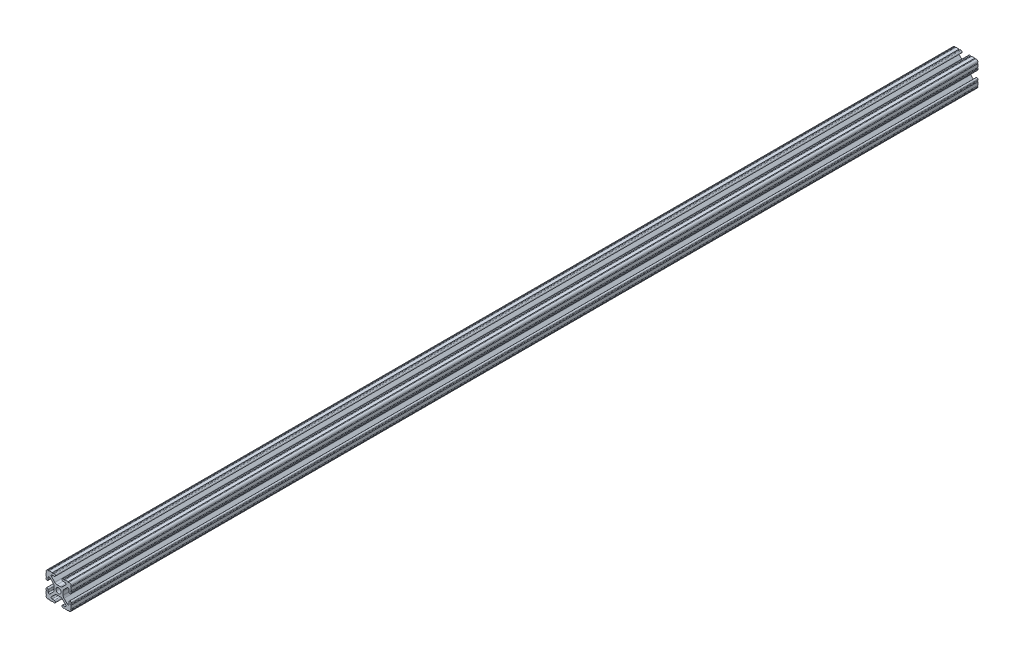
SolidWorks part; units mm, degrees
ref_plane "Front Plane" through (0, 0, 0) normal (0, 0, 1) x (1, 0, 0)
ref_plane "Top Plane" through (0, 0, 0) normal (0, 1, 0) x (1, 0, 0)
ref_plane "Right Plane" through (0, 0, 0) normal (1, 0, 0) x (0, 0, -1)
sketch "Sketch1" plane through (0, 0, 0) normal (0, 0, 1) x (1, 0, 0)
  line L0 (-12.7, -6.3331) -> (-12.7, -9.5504)
  line L1 (-9.5504, -12.7) -> (-6.3331, -12.7)
  line L2 (-5.3171, -12.7) -> (-4.3434, -12.7)
  line L3 (-4.3434, -10.4902) -> (-6.4748, -10.4902)
  line L4 (-7.1932, -8.7558) -> (-3.8632, -5.4257)
  line L5 (-1.6181, -4.4958) -> (1.6181, -4.4958)
  line L6 (3.8632, -5.4257) -> (7.1932, -8.7558)
  line L7 (6.4748, -10.4902) -> (4.3434, -10.4902)
  line L8 (4.3434, -12.7) -> (5.3171, -12.7)
  line L9 (6.3331, -12.7) -> (9.5504, -12.7)
  line L10 (12.7, -9.5504) -> (12.7, -6.3331)
  line L11 (12.7, -5.3171) -> (12.7, -4.3434)
  line L12 (10.4902, -4.3434) -> (10.4902, -6.4748)
  line L13 (8.7558, -7.1932) -> (5.4257, -3.8632)
  line L14 (4.4958, -1.6181) -> (4.4958, 1.6181)
  line L15 (5.4257, 3.8632) -> (8.7558, 7.1932)
  line L16 (10.4902, 6.4748) -> (10.4902, 4.3434)
  line L17 (12.7, 4.3434) -> (12.7, 5.3171)
  line L18 (12.7, 6.3331) -> (12.7, 9.5504)
  line L19 (9.5504, 12.7) -> (6.3331, 12.7)
  line L20 (5.3171, 12.7) -> (4.3434, 12.7)
  line L21 (4.3434, 10.4902) -> (6.4748, 10.4902)
  line L22 (7.1932, 8.7558) -> (3.8632, 5.4257)
  line L23 (1.6181, 4.4958) -> (-1.6181, 4.4958)
  line L24 (-3.8632, 5.4257) -> (-7.1932, 8.7558)
  line L25 (-6.4748, 10.4902) -> (-4.3434, 10.4902)
  line L26 (-4.3434, 12.7) -> (-5.3171, 12.7)
  line L27 (-6.3331, 12.7) -> (-9.5504, 12.7)
  line L28 (-12.7, 9.5504) -> (-12.7, 6.3331)
  line L29 (-12.7, 5.3171) -> (-12.7, 4.3434)
  line L30 (-10.4902, 4.3434) -> (-10.4902, 6.4748)
  line L31 (-8.7558, 7.1932) -> (-5.4257, 3.8632)
  line L32 (-4.4958, 1.6181) -> (-4.4958, -1.6181)
  line L33 (-5.4257, -3.8632) -> (-8.7558, -7.1932)
  line L34 (-10.4902, -6.4748) -> (-10.4902, -4.3434)
  line L35 (-12.7, -4.3434) -> (-12.7, -5.3171)
  circle A0 centre (0, 0) radius 2.6035
  arc A1 (-12.7, -5.3171) -> (-12.7, -6.3331) centre (-12.7, -5.8251) cw
  arc A2 (-12.7, -9.5504) -> (-12.6998, -10.5664) centre (-12.7, -10.0584) cw
  arc A3 (-12.6998, -10.5664) -> (-10.5664, -12.6998) centre (-10.5918, -10.5918) ccw
  arc A4 (-10.5664, -12.6998) -> (-9.5504, -12.7) centre (-10.0584, -12.7) cw
  arc A5 (-6.3331, -12.7) -> (-5.3171, -12.7) centre (-5.8251, -12.7) cw
  arc A6 (-4.3434, -12.7) -> (-4.3434, -10.4902) centre (-4.3434, -11.5951) ccw
  arc A7 (-6.4748, -10.4902) -> (-7.1932, -8.7558) centre (-6.4748, -9.4742) cw
  arc A8 (-3.8632, -5.4257) -> (-1.6181, -4.4958) centre (-1.6181, -7.6708) cw
  arc A9 (1.6181, -4.4958) -> (3.8632, -5.4257) centre (1.6181, -7.6708) cw
  arc A10 (7.1932, -8.7558) -> (6.4748, -10.4902) centre (6.4748, -9.4742) cw
  arc A11 (4.3434, -10.4902) -> (4.3434, -12.7) centre (4.3434, -11.5951) ccw
  arc A12 (5.3171, -12.7) -> (6.3331, -12.7) centre (5.8251, -12.7) cw
  arc A13 (9.5504, -12.7) -> (10.5664, -12.6998) centre (10.0584, -12.7) cw
  arc A14 (10.5664, -12.6998) -> (12.6998, -10.5664) centre (10.5918, -10.5918) ccw
  arc A15 (12.6998, -10.5664) -> (12.7, -9.5504) centre (12.7, -10.0584) cw
  arc A16 (12.7, -6.3331) -> (12.7, -5.3171) centre (12.7, -5.8251) cw
  arc A17 (12.7, -4.3434) -> (10.4902, -4.3434) centre (11.5951, -4.3434) ccw
  arc A18 (10.4902, -6.4748) -> (8.7558, -7.1932) centre (9.4742, -6.4748) cw
  arc A19 (5.4257, -3.8632) -> (4.4958, -1.6181) centre (7.6708, -1.6181) cw
  arc A20 (4.4958, 1.6181) -> (5.4257, 3.8632) centre (7.6708, 1.6181) cw
  arc A21 (8.7558, 7.1932) -> (10.4902, 6.4748) centre (9.4742, 6.4748) cw
  arc A22 (10.4902, 4.3434) -> (12.7, 4.3434) centre (11.5951, 4.3434) ccw
  arc A23 (12.7, 5.3171) -> (12.7, 6.3331) centre (12.7, 5.8251) cw
  arc A24 (12.7, 9.5504) -> (12.6998, 10.5664) centre (12.7, 10.0584) cw
  arc A25 (12.6998, 10.5664) -> (10.5664, 12.6998) centre (10.5918, 10.5918) ccw
  arc A26 (10.5664, 12.6998) -> (9.5504, 12.7) centre (10.0584, 12.7) cw
  arc A27 (6.3331, 12.7) -> (5.3171, 12.7) centre (5.8251, 12.7) cw
  arc A28 (4.3434, 12.7) -> (4.3434, 10.4902) centre (4.3434, 11.5951) ccw
  arc A29 (6.4748, 10.4902) -> (7.1932, 8.7558) centre (6.4748, 9.4742) cw
  arc A30 (3.8632, 5.4257) -> (1.6181, 4.4958) centre (1.6181, 7.6708) cw
  arc A31 (-1.6181, 4.4958) -> (-3.8632, 5.4257) centre (-1.6181, 7.6708) cw
  arc A32 (-7.1932, 8.7558) -> (-6.4748, 10.4902) centre (-6.4748, 9.4742) cw
  arc A33 (-4.3434, 10.4902) -> (-4.3434, 12.7) centre (-4.3434, 11.5951) ccw
  arc A34 (-5.3171, 12.7) -> (-6.3331, 12.7) centre (-5.8251, 12.7) cw
  arc A35 (-9.5504, 12.7) -> (-10.5664, 12.6998) centre (-10.0584, 12.7) cw
  arc A36 (-10.5664, 12.6998) -> (-12.6998, 10.5664) centre (-10.5918, 10.5918) ccw
  arc A37 (-12.6998, 10.5664) -> (-12.7, 9.5504) centre (-12.7, 10.0584) cw
  arc A38 (-12.7, 6.3331) -> (-12.7, 5.3171) centre (-12.7, 5.8251) cw
  arc A39 (-12.7, 4.3434) -> (-10.4902, 4.3434) centre (-11.5951, 4.3434) ccw
  arc A40 (-10.4902, 6.4748) -> (-8.7558, 7.1932) centre (-9.4742, 6.4748) cw
  arc A41 (-5.4257, 3.8632) -> (-4.4958, 1.6181) centre (-7.6708, 1.6181) cw
  arc A42 (-4.4958, -1.6181) -> (-5.4257, -3.8632) centre (-7.6708, -1.6181) cw
  arc A43 (-8.7558, -7.1932) -> (-10.4902, -6.4748) centre (-9.4742, -6.4748) cw
  arc A44 (-10.4902, -4.3434) -> (-12.7, -4.3434) centre (-11.5951, -4.3434) ccw
extrude "Boss-Extrude1" add sketch "Sketch1" against normal blind 914.4
